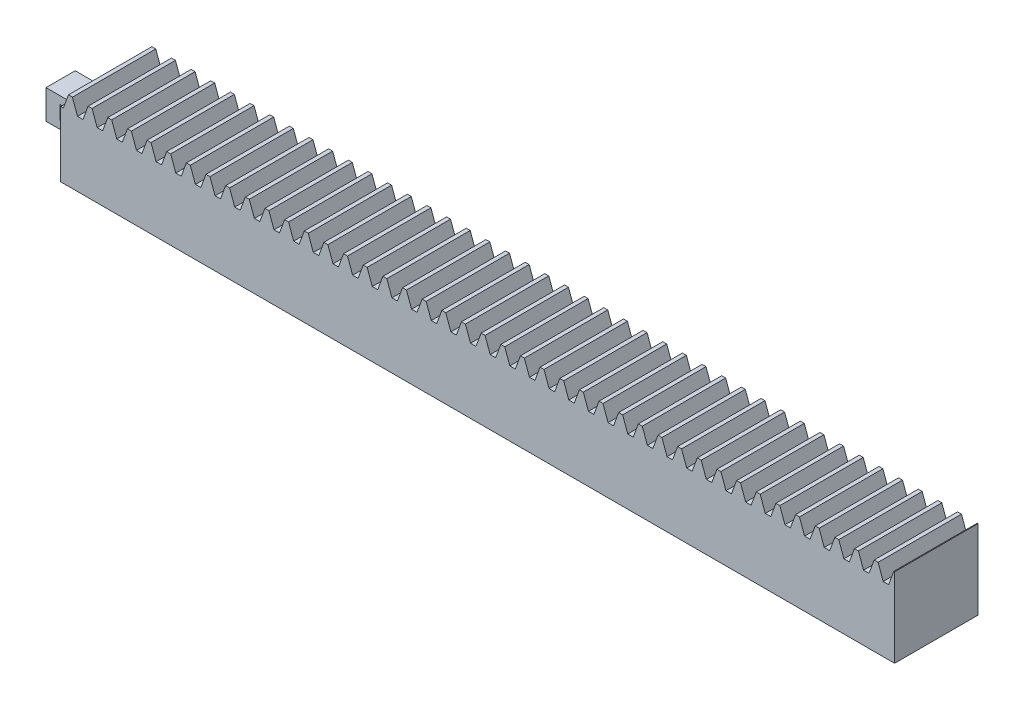
SolidWorks part; units mm, degrees
extrude "Blank" add sketch "BlankSke" against normal blind 20
sketch "BlankSke" plane through (0, 0, 0) normal (0, 0, 1) x (1, 0, 0)
  line L1 (0, 0) -> (200, 0)
  line L2 (0, 0) -> (0, 19)
  line L3 (0, 19) -> (200, 19)
  line L4 (200, 0) -> (200, 19)
  dimension "Length" = 200
  dimension "Blank_height" = 19
ref_plane "Plane1" through (0, 0, 0) normal (0, 0, 1) x (1, 0, 0)
ref_plane "Plane2" through (0, 0, 0) normal (0, 1, 0) x (1, 0, 0)
ref_plane "Plane3" through (0, 0, 0) normal (1, 0, 0) x (0, 0, -1)
other "Configuration Table"
sketch "HoldingSke" plane through (0, 0, 0) normal (0, 1, 0) x (1, 0, 0)
  line L0 (0, 0) -> (0.0928, 0.6602)
  line L1 (-15, 0) -> (100, 0) construction
  line L2 (0, 0) -> (-2.1039, 2.3779)
  line L3 (0, 0) -> (-11.863, 4.5341)
  line L4 (0, 0) -> (6.2122, 5.9991)
  line L5 (0, 0) -> (-23.7986, -8.8762)
  line L6 (0, 0) -> (-10.5278, -7.1032)
  line L9 (-71.009, 38.7566) -> (116.9296, 107.1606)
  line L10 (-76.2, 3.8779) -> (-58.7, 3.8779)
  line L11 (0, 0) -> (-20, 0)
  line L12 (-76.2, 101.6) -> (-76.147, 101.6)
  line L13 (24.9733, 27.94) -> (52.9518, 28.4284)
  line L14 (24.9733, 27.94) -> (24.9743, 27.94)
  line L15 (24.9733, 27.94) -> (100.4006, 29.5858)
  circle A0 centre (0, 0) radius 19.05
  circle A1 centre (0, 0) radius 8.75
  circle A2 centre (0, 0) radius 12.7
  dimension "MPH" = 17.5
  dimension "Diameter" = 38.1
  dimension "Num_teeth" = 44
  dimension "Pitch" = 0.6667
  dimension "Show_teeth" = 998
  dimension "Thickness" = 12.7
  dimension "Ap" = 20
  dimension "Pitch_height" = 17.5
  dimension "Width" = 20
  dimension "Backlash" = 0.053
  dimension "Addendum_fac" = 1
  dimension "Dedendum_fac" = 1.25
  dimension "Clearance_fac" = 0.25
  dimension "Dedendum_add" = 0.001
  dimension "Length" = 200
  dimension "Module" = 1.5
sketch "TooCutSkeIll" plane through (0, 0, 0) normal (0, 0, 1) x (1, 0, 0)
  line L0 (-1.8687, 18.9605) -> (-0.7447, 15.8724)
  line L1 (-0.3914, 15.625) -> (0.3914, 15.625)
  line L2 (0.7447, 15.8724) -> (1.8687, 18.9605)
  line L3 (200, 19) -> (0, 19) construction
  line L4 (0, 0) -> (0, 64.897) construction
  line L5 (-13.208, 17.5) -> (12.954, 17.5) construction
  line L6 (0, 0) -> (200, 0) construction
  line L7 (1.3371, 17.5) -> (1.3371, 48.7463) construction
  line L8 (-1.3371, 17.5) -> (-1.3371, 48.7463) construction
  line L9 (1.9251, 19) -> (1.9251, 19.0254)
  line L10 (-1.9251, 19) -> (-1.9251, 19.0254)
  line L11 (-1.9251, 19.0254) -> (1.9251, 19.0254)
  arc A0 (0.3914, 15.625) -> (0.7447, 15.8724) centre (0.3914, 16.001) ccw
  arc A1 (-0.7447, 15.8724) -> (-0.3914, 15.625) centre (-0.3914, 16.001) ccw
  arc A2 (1.9251, 19) -> (1.8687, 18.9605) centre (1.9251, 18.94) ccw
  arc A3 (-1.8687, 18.9605) -> (-1.9251, 19) centre (-1.9251, 18.94) ccw
  dimension "Pitch_height" = 17.5
  dimension "Addendum_plus" = 1.5254
  dimension "Pressure_angle" = 20
  dimension "Gap_width" = 2.6742
  dimension "Dedendum" = 1.875
extrude "ToothCutIll" [suppressed] cut sketch "TooCutSkeIll" against normal through all
sketch "TooCutSkeSim" plane through (0, 0, 0) normal (0, 0, 1) x (1, 0, 0)
  line L0 (0.6547, 15.625) -> (-0.6547, 15.625)
  line L1 (1.8923, 19.0254) -> (0.6547, 15.625)
  line L2 (0, 17.4625) -> (0, 53.467) construction
  line L3 (1.8923, 19.0254) -> (-1.8923, 19.0254)
  line L6 (-1.8923, 19.0254) -> (-0.6547, 15.625)
  line L9 (-1.3371, 17.5) -> (1.3371, 17.5) construction
  line L10 (0, 0) -> (200, 0) construction
  line L11 (1.3371, 17.5) -> (1.3371, 53.467) construction
  line L12 (-1.3371, 17.5) -> (-1.3371, 53.467) construction
  dimension "Pitch_height" = 17.5
  dimension "Addendum_plus" = 1.5254
  dimension "Pressure_angle" = 20
  dimension "Gap_width" = 2.6742
  dimension "Dedendum" = 1.875
extrude "ToothCutSim" cut sketch "TooCutSkeSim" against normal through all
pattern_linear "TeethCuts" count 43 spacing 4.7124 along (1, 0, 0) of "ToothCutIll", "ToothCutSim"
sketch "Sketch3" plane through (0, 0, 0) normal (-1, 0, 0) x (0, 0, 1)
  line L1 (-13.5, 11.3125) -> (-6.5, 11.3125)
  line L2 (-13.5, 11.3125) -> (-13.5, 4.3125)
  line L3 (-13.5, 4.3125) -> (-6.5, 4.3125)
  line L4 (-6.5, 11.3125) -> (-6.5, 4.3125)
  line L5 (-20, 15.625) -> (0, 0) construction
  line L6 (-20, 0) -> (0, 15.625) construction
  line L7 (-13.5, 11.3125) -> (-6.5, 4.3125) construction
  line L8 (-13.5, 4.3125) -> (-6.5, 11.3125) construction
  point P12 (-10, 7.8125)
  point P14 (-10, 7.8125)
  dimension "D1" = 7
extrude "Boss-Extrude2" add sketch "Sketch3" along normal blind 10
sketch "Sketch4" plane through (0, 0, -13.5) normal (0, 0, -1) x (-1, 0, 0)
  line L0 (0, 7.8125) -> (10, 7.8125) construction
  line L1 (3.35, 9.4625) -> (6.65, 9.4625)
  line L2 (3.35, 9.4625) -> (3.35, 6.1625)
  line L3 (3.35, 6.1625) -> (6.65, 6.1625)
  line L4 (6.65, 9.4625) -> (6.65, 6.1625)
  line L5 (0, 11.3125) -> (0, 4.3125) construction
  line L6 (10, 11.3125) -> (10, 4.3125) construction
  line L7 (3.35, 9.4625) -> (6.65, 6.1625) construction
  point P11 (5, 7.8125)
  point P12 (0, 0)
  dimension "D1" = 3.3
  dimension "D2" = 3.35
extrude "Cut-Extrude1" cut sketch "Sketch4" against normal blind 25
equation "' \"Module@HoldingSke\" = 6.35"
equation "' \"Num_teeth@HoldingSke\" = 12"
equation "' \"Ap@HoldingSke\" =  20"
equation "' \"Ap@HoldingSke\" = 20"
equation "' \"Width@HoldingSke\" = 0.25 * 25.4"
equation "' \"Show_teeth@HoldingSke\" = 500"
equation "' \"Backlash@HoldingSke\" = 0.009 * 25.4"
equation "' \"Addendum_fac@HoldingSke\" = 1.0"
equation "' \"Dedendum_fac@HoldingSke\" = 1.25"
equation "' \"Dedendum_add@HoldingSke\" = 0.00005 * 25.4"
equation "' \"Clearance_fac@HoldingSke\" = 0.25"
equation "' \"Pitch_height@HoldingSke\" = 1 * 25.4"
equation "' \"Length@HoldingSke\" = 4.71 * 25.4"
equation "\"Pitch@HoldingSke\" = 1 / \"Module@HoldingSke\""
equation "\"MPH@HoldingSke\" = \"Dedendum_fac@HoldingSke\" / \"Pitch@HoldingSke\" + 2 * \"Dedendum_add@HoldingSke\" + 0.002 * 25.4"
equation "\"MPH@HoldingSke\" = ((sgn( \"MPH@HoldingSke\" - \"Pitch_height@HoldingSke\")+1)*( \"MPH@HoldingSke\" - \"Pitch_height@HoldingSke\"))/2 + \"Pitch_height@HoldingSke\""
equation "\"Blank_height@BlankSke\" = \"Pitch_height@HoldingSke\" + \"Addendum_fac@HoldingSke\"  / \"Pitch@HoldingSke\" "
equation "\"Length@BlankSke\" =  \"Length@HoldingSke\""
equation "\"Face_width@Blank\" = \"Width@HoldingSke\""
equation "\"Pressure_angle@TooCutSkeIll\" = \"Ap@HoldingSke\""
equation "\"Addendum_plus@TooCutSkeIll\" =  \"Addendum_fac@HoldingSke\"  / \"Pitch@HoldingSke\" + 0.001 *25.4"
equation "\"Dedendum@TooCutSkeIll\" = \"Dedendum_fac@HoldingSke\"  / \"Pitch@HoldingSke\""
equation "\"Pitch_height@TooCutSkeIll\" =  \"MPH@HoldingSke\""
equation "\"Gap_width@TooCutSkeIll\" = 3.14159265 / 2 / \"Pitch@HoldingSke\" + 6 * \"Backlash@HoldingSke\""
equation "\"Pressure_angle@TooCutSkeSim\" = \"Ap@HoldingSke\""
equation "\"Addendum_plus@TooCutSkeSim\" =  \"Addendum_fac@HoldingSke\"  / \"Pitch@HoldingSke\" + 0.001 * 25.4"
equation "\"Dedendum@TooCutSkeSim\" = \"Dedendum_fac@HoldingSke\"  / \"Pitch@HoldingSke\""
equation "\"Pitch_height@TooCutSkeSim\" =  \"MPH@HoldingSke\""
equation "\"Gap_width@TooCutSkeSim\" = 3.14159265 / 2 / \"Pitch@HoldingSke\" + 6 * \"Backlash@HoldingSke\""
equation "\"Root_fillet@TooCutSkeIll\" = \"Clearance_fac@HoldingSke\" / \"Pitch@HoldingSke\" + \"Dedendum_add@HoldingSke\""
equation "\"Break_rad@TooCutSkeIll\" = 0.02 / \"Pitch@HoldingSke\" * 2"
equation "\"Linear_pitch@TeethCuts\" = 3.14159265 / \"Pitch@HoldingSke\""
equation "\"Num_teeth@HoldingSke\" = int( ( \"Length@HoldingSke\" + 0 ) / (3.14159265 / \"Pitch@HoldingSke\")) + 0.9999  + 1"
equation " \"Num_teeth@TeethCuts\" = int( \"Show_teeth@HoldingSke\" ) + 1"
equation " \"Num_teeth@TeethCuts\" = ((sgn( \"Num_teeth@TeethCuts\" - \"Num_teeth@HoldingSke\" )-1)*( \"Num_teeth@TeethCuts\" - \"Num_teeth@HoldingSke\" ))/-2+ \"Num_teeth@HoldingSke\""
equation " \"Num_teeth@TeethCuts\" = ((sgn( \"Num_teeth@TeethCuts\" - 2.0)+1)*( \"Num_teeth@TeethCuts\" - 2.0))/2 +2.0"
